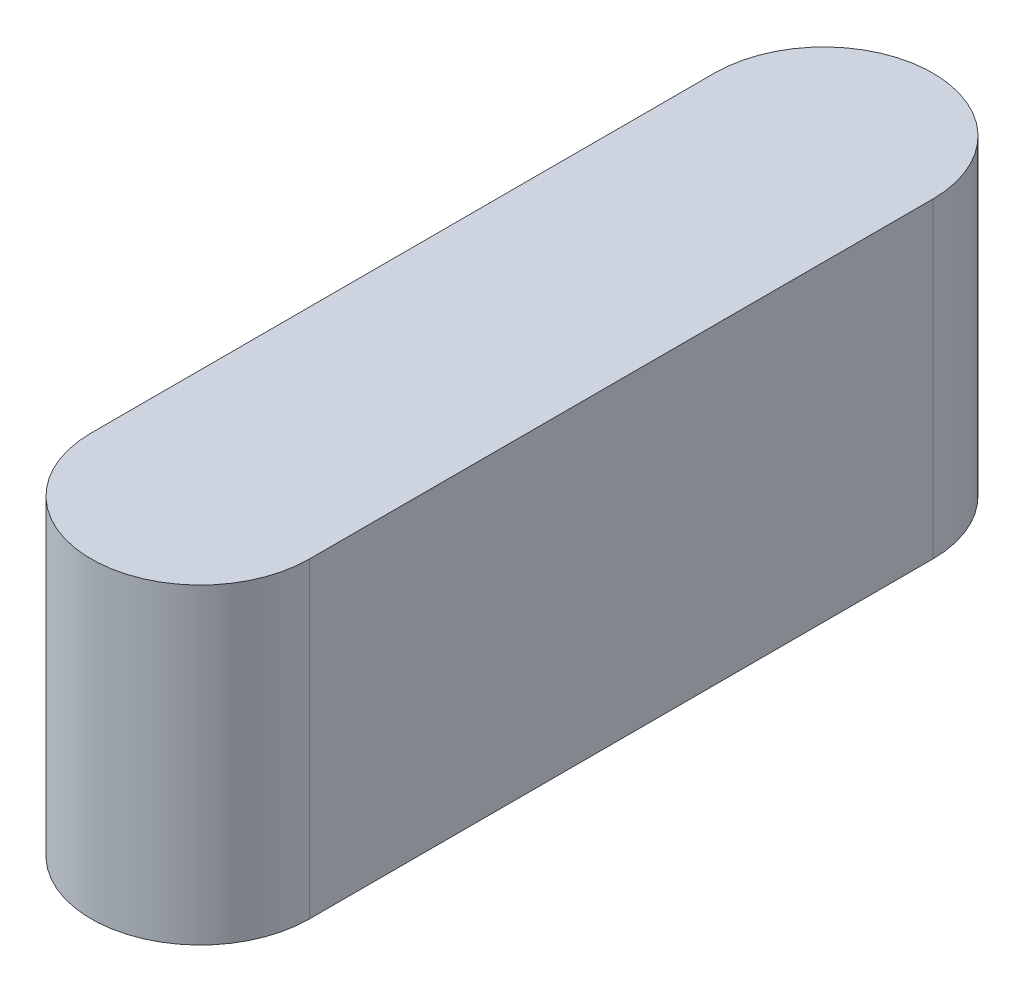
SolidWorks part; units mm, degrees
ref_plane "Front Plane" through (0, 0, 0) normal (0, 0, 1) x (1, 0, 0)
ref_plane "Top Plane" through (0, 0, 0) normal (0, 1, 0) x (1, 0, 0)
ref_plane "Right Plane" through (0, 0, 0) normal (1, 0, 0) x (0, 0, -1)
sketch "Sketch3" plane through (0, 0, 0) normal (0, 1, 0) x (1, 0, 0)
  line L0 (0, -8.714) -> (0, -18.714) construction
  line L1 (1.75, -8.714) -> (1.75, -18.714)
  line L2 (-1.75, -8.714) -> (-1.75, -18.714)
  arc A0 (1.75, -8.714) -> (-1.75, -8.714) centre (0, -8.714) ccw
  arc A1 (-1.75, -18.714) -> (1.75, -18.714) centre (0, -18.714) ccw
  point P3 (0, -13.714)
  dimension "D1" = 3.5
  dimension "D2" = 10
extrude "Boss-Extrude1" add sketch "Sketch3" along normal blind 5
